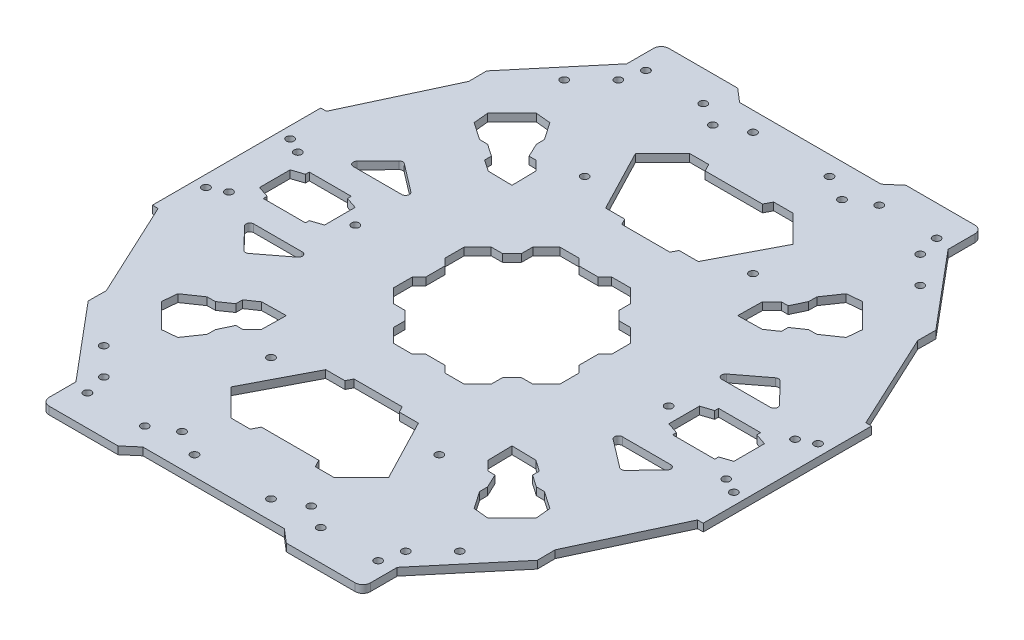
SolidWorks part; units mm, degrees
ref_plane "Front Plane" through (0, 0, 0) normal (0, 0, 1) x (1, 0, 0)
ref_plane "Top Plane" through (0, 0, 0) normal (0, 1, 0) x (1, 0, 0)
ref_plane "Right Plane" through (0, 0, 0) normal (1, 0, 0) x (0, 0, -1)
sketch "Sketch2" plane through (0, 0, 0) normal (0, 1, 0) x (1, 0, 0)
  line L0 (0, 78) -> (-18.5, 78)
  line L1 (-18.5, 78) -> (-22, 81)
  line L2 (-22, 81) -> (-40, 81)
  line L4 (-42, 72) -> (-58.7125, 52.0828)
  line L5 (-58.7125, 52.0828) -> (-58.6681, 47.3908)
  line L6 (-58.6681, 47.3908) -> (-70.5014, 22.0142)
  line L7 (-70.5014, 22.0142) -> (-72, 22)
  line L8 (-72, 22) -> (-72, 0)
  line L9 (-72, 0) -> (-62, 0) construction
  line L10 (0, 20) -> (0, 35) construction
  line L11 (0, 78) -> (0, 58)
  line L12 (-20, 0) -> (-45, 0)
  line L13 (-42, 79) -> (-42, 72)
  line L23 (-62, 0) -> (-62, 4)
  line L24 (-62, 4) -> (-59, 5)
  line L25 (-59, 5) -> (-59, 6)
  line L26 (-59, 6) -> (-48, 6)
  line L27 (-48, 6) -> (-48, 5)
  line L28 (-48, 5) -> (-45, 4)
  line L29 (-45, 4) -> (-45, 0)
  line L30 (-59, 5) -> (-48, 5) construction
  line L31 (-62, 4) -> (-45, 4) construction
  line L32 (-62, 0) -> (-72, 0)
  line L33 (-45, 0) -> (-20, 0) construction
  line L34 (-20, 0) -> (-20, 2.5)
  line L35 (-20, 2.5) -> (-21.7678, 4.2678)
  line L36 (-21.7678, 4.2678) -> (-21.7678, 9.2678)
  line L37 (-21.7678, 9.2678) -> (-18.2322, 12.8033)
  line L38 (-18.2322, 12.8033) -> (-15.2322, 12.8033)
  line L39 (-15.2322, 12.8033) -> (-12.8033, 15.2322)
  line L40 (-12.8033, 15.2322) -> (-12.8033, 18.2322)
  line L41 (-12.8033, 18.2322) -> (-9.2678, 21.7678)
  line L42 (-9.2678, 21.7678) -> (-4.2678, 21.7678)
  line L43 (-4.2678, 21.7678) -> (-2.5, 20)
  line L44 (-2.5, 20) -> (0, 20)
  line L45 (0, 58) -> (-7.5, 58)
  line L46 (-7.5, 58) -> (-8.5, 59.9227)
  line L47 (-8.5, 59.9227) -> (-13.5, 59.9227)
  line L48 (-13.5, 59.9227) -> (-20.5711, 52.8516)
  line L49 (-20.5711, 52.8516) -> (-12.1097, 36.5829)
  line L50 (-12.1097, 36.5829) -> (-7.1097, 36.5829)
  line L51 (-7.1097, 36.5829) -> (-6.2864, 35)
  line L52 (-6.2864, 35) -> (0, 35)
  line L53 (0, 58) -> (0, 78) construction
  line L54 (0, 35) -> (0, 20)
  line L55 (0, 20) -> (0, 0) construction
  line L56 (0, 0) -> (-20, 0) construction
  line L57 (-38, 73) -> (-23, 73) construction
  line L58 (-23, 73) -> (-10, 73) construction
  line L59 (-10, 73) -> (0, 73) construction
  line L60 (-39.4554, 67.254) -> (-46.5264, 60.1829) construction
  line L61 (-39.4554, 67.254) -> (-43.2856, 70.4679) construction
  line L62 (-54.5154, 13) -> (-41.8398, 13)
  line L63 (-41.2331, 14.7949) -> (-48.5098, 20.3496)
  line L64 (-49.8336, 20.2517) -> (-55.2325, 14.697)
  line L65 (0, 0) -> (-100.3745, 100.3745) construction
  line L66 (-49.0044, 42.6404) -> (-42.6404, 49.0044)
  line L67 (-42.6404, 49.0044) -> (-38.7306, 48.6301)
  line L68 (-38.7306, 48.6301) -> (-35.6207, 44.106)
  line L69 (-35.6207, 44.106) -> (-35.5818, 41.9458)
  line L70 (-35.5818, 41.9458) -> (-33.8755, 38.328)
  line L71 (-33.8755, 38.328) -> (-32.1077, 38.328)
  line L72 (-32.1077, 38.328) -> (-29.6107, 35.831)
  line L73 (-29.6107, 35.831) -> (-29.4969, 29.4969)
  line L74 (-29.4969, 29.4969) -> (-35.831, 29.6107)
  line L75 (-35.831, 29.6107) -> (-38.7906, 31.6451)
  line L76 (-38.7906, 31.6451) -> (-38.7906, 33.4129)
  line L77 (-38.7906, 33.4129) -> (-41.9458, 35.5818)
  line L78 (-41.9458, 35.5818) -> (-44.106, 35.6207)
  line L79 (-44.106, 35.6207) -> (-48.6301, 38.7306)
  line L80 (-48.6301, 38.7306) -> (-49.0044, 42.6404)
  line L81 (-38.7306, 48.6301) -> (-48.6301, 38.7306) construction
  line L82 (-44.106, 35.6207) -> (-35.6207, 44.106) construction
  line L83 (-35.5818, 41.9458) -> (-41.9458, 35.5818) construction
  line L84 (-38.7906, 33.4129) -> (-33.8755, 38.328) construction
  line L85 (-32.1077, 38.328) -> (-38.7906, 31.6451) construction
  line L86 (-35.831, 29.6107) -> (-29.6107, 35.831) construction
  arc A0 (-40, 81) -> (-42, 79) centre (-40, 79) ccw
  circle A1 centre (-38, 73) radius 1
  circle A2 centre (-23, 73) radius 1
  circle A3 centre (-10, 73) radius 1
  circle A4 centre (-16.8822, 69.3859) radius 1
  circle A5 centre (-46.5264, 60.1829) radius 1
  circle A6 centre (-40.9575, 0) radius 1
  circle A7 centre (-39.4554, 67.254) radius 1
  arc A8 (-41.8398, 13) -> (-41.2331, 14.7949) centre (-41.8398, 14) ccw
  arc A9 (-48.5098, 20.3496) -> (-49.8336, 20.2517) centre (-49.1165, 19.5548) ccw
  arc A10 (-54.5154, 13) -> (-55.2325, 14.697) centre (-54.5154, 14) cw
  circle A11 centre (-69, 11) radius 1
  circle A12 centre (-65, 9) radius 1
  circle A13 centre (-22, 41) radius 1
  point P25 (-42, 81)
  point P63 (-38.8818, 13)
  point P68 (-49.2151, 20.8881)
  point P71 (-56.8818, 13)
  point P93 (-43.6804, 43.6804)
  point P94 (-39.8633, 39.8633)
  point P95 (-45.8224, 45.8224)
  point P96 (-38.7638, 38.7638)
  point P99 (-32.7209, 32.7209)
  dimension "D13" = 2
  dimension "D41" = 15
  dimension "D52" = 1
  dimension "D63" = 41
  dimension "D1" = 81
  dimension "D2" = 72
  dimension "D3" = 18.5
  dimension "D4" = 20
  dimension "D5" = 9
  dimension "D6" = 22
  dimension "D7" = 26
  dimension "D8" = 28
  dimension "D9" = 50
  dimension "D10" = 25
  dimension "D11" = 42
  dimension "D12" = 3
  dimension "D14" = 2.5
  dimension "D15" = 20
  dimension "D16" = 2.5
  dimension "D17" = 45
  dimension "D18" = 5
  dimension "D19" = 2.5
  dimension "D20" = 5
  dimension "D21" = 20
  dimension "D22" = 17
  dimension "D23" = 6
  dimension "D24" = 3
  dimension "D25" = 3
  dimension "D26" = 4
  dimension "D27" = 1
  dimension "D28" = 10
  dimension "D29" = 5
  dimension "D30" = 2.5
  dimension "D31" = 3
  dimension "D32" = 5
  dimension "D33" = 20
  dimension "D34" = 23
  dimension "D35" = 5
  dimension "D36" = 7.5
  dimension "D37" = 1
  dimension "D38" = 10
  dimension "D39" = 45
  dimension "D40" = 5
  dimension "D42" = 13
  dimension "D43" = 10
  dimension "D44" = 5
  dimension "D45" = 5
  dimension "D46" = 10
  dimension "D47" = 2
  dimension "D48" = 18
  dimension "D49" = 13
  dimension "D50" = 11
  dimension "D51" = 7
  dimension "D53" = 11
  dimension "D54" = 9
  dimension "D55" = 3
  dimension "D56" = 4
  dimension "D57" = 45
  dimension "D58" = 14
  dimension "D59" = 9
  dimension "D60" = 9
  dimension "D61" = 12
  dimension "D62" = 45
  dimension "D64" = 22
extrude "Boss-Extrude1" add sketch "Sketch2" along normal blind 2 contours A6 L12 L34 L35 L36 L37 L38 L39 L40 L41 L42 L43 L44 L54 L52 L51 L50 L49 L48 L47 L46 L45 L11 L0 L1 L2 A0 L13 L4 L5 L6 L7 L8 L32 L23 L24 L25 L26 L27 L28 L29 A7 A5 A4 A3
mirror "Mirror2" about plane through (0, 0, 0) normal (1, 0, 0) of "Boss-Extrude1"
